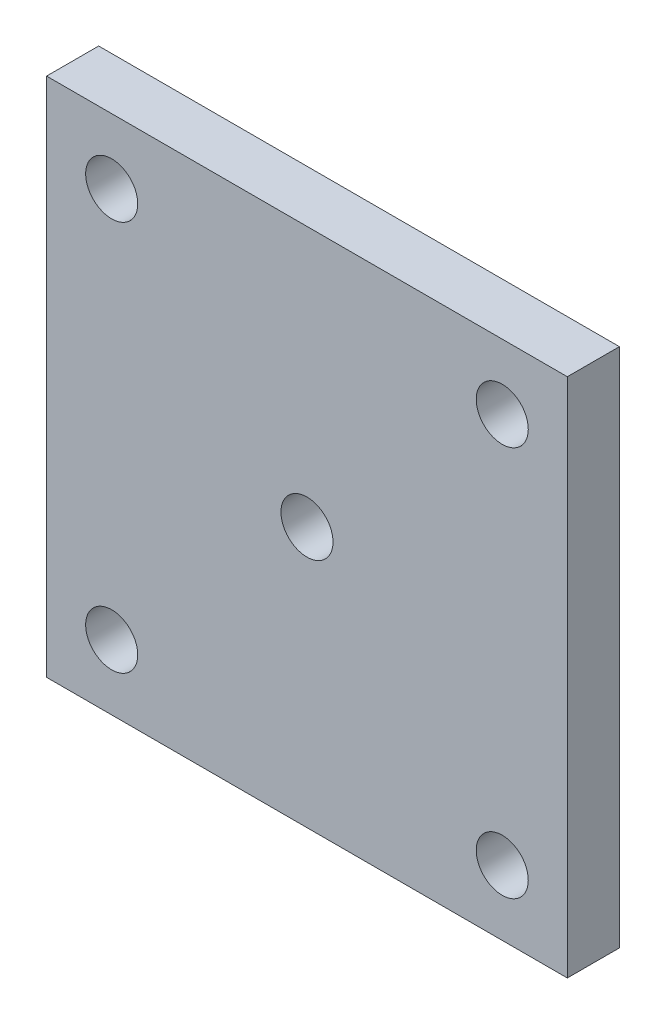
SolidWorks part; units mm, degrees
ref_plane "Front Plane" through (0, 0, 0) normal (0, 0, 1) x (1, 0, 0)
ref_plane "Top Plane" through (0, 0, 0) normal (0, 1, 0) x (1, 0, 0)
ref_plane "Right Plane" through (0, 0, 0) normal (1, 0, 0) x (0, 0, -1)
sketch "Sketch1" plane through (0, 0, 0) normal (0, 0, 1) x (1, 0, 0)
  line L1 (20, -20) -> (-20, -20)
  line L2 (20, -20) -> (20, 20)
  line L3 (20, 20) -> (-20, 20)
  line L4 (-20, -20) -> (-20, 20)
  line L5 (20, -20) -> (-20, 20) construction
  line L6 (20, 20) -> (-20, -20) construction
  point P0 (0, 0)
  dimension "D1" = 40
  dimension "40" = 40
extrude "Boss-Extrude1" add sketch "Sketch1" along normal blind 4
sketch "Sketch2" plane through (0, 0, 4) normal (0, 0, 1) x (1, 0, 0)
  line L0 (-20, 20) -> (-20, -20) construction
  line L1 (20, 20) -> (-20, 20) construction
  circle A0 centre (-15, 15) radius 2
  circle A1 centre (15, 15) radius 2
  circle A2 centre (15, -15) radius 2
  circle A3 centre (-15, -15) radius 2
  point P15 (0, 0)
  dimension "D1" = 4
  dimension "D2" = 5
  dimension "D3" = 5
  dimension "D4" = 4
extrude "Cut-Extrude1" cut sketch "Sketch2" against normal blind 4
sketch "Sketch3" plane through (0, 0, 4) normal (0, 0, 1) x (1, 0, 0)
  circle A0 centre (0, 0) radius 2
  dimension "D1" = 4
extrude "Cut-Extrude2" cut sketch "Sketch3" against normal blind 4
